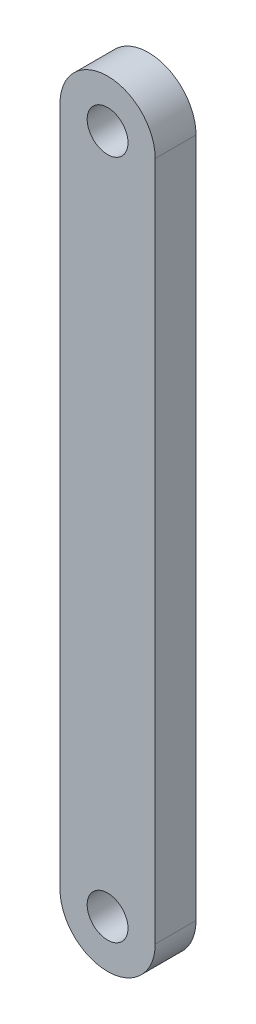
SolidWorks part; units mm, degrees
material "ABS"
ref_plane "Front Plane" through (0, 0, 0) normal (0, 0, 1) x (1, 0, 0)
ref_plane "Top Plane" through (0, 0, 0) normal (0, 1, 0) x (1, 0, 0)
ref_plane "Right Plane" through (0, 0, 0) normal (1, 0, 0) x (0, 0, -1)
sketch "Sketch1" plane through (0, 0, 0) normal (0, 0, 1) x (1, 0, 0)
  line L0 (0, 25) -> (0, -25) construction
  line L1 (3.5, 25) -> (3.5, -25)
  line L2 (-3.5, 25) -> (-3.5, -25)
  arc A0 (3.5, 25) -> (-3.5, 25) centre (0, 25) ccw
  arc A1 (-3.5, -25) -> (3.5, -25) centre (0, -25) ccw
  circle A2 centre (0, -25) radius 1.5
  circle A3 centre (0, 25) radius 1.5
  point P3 (0, 0)
  dimension "D3" = 3
  dimension "D1" = 50
  dimension "D2" = 7
extrude "Boss-Extrude1" add sketch "Sketch1" along normal mid plane 3
